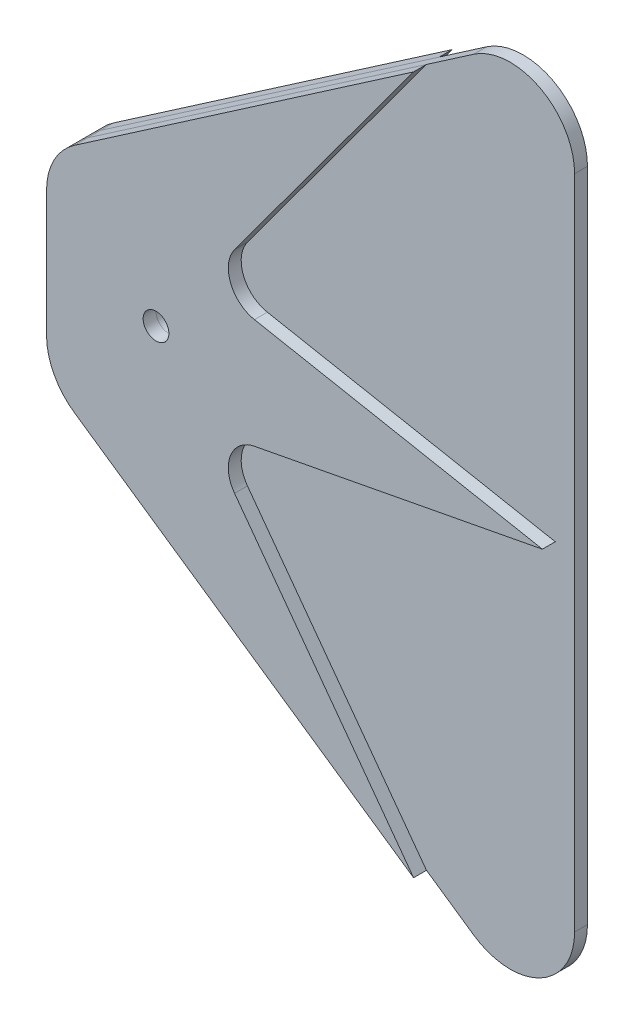
SolidWorks part; units mm, degrees
material "Silicon Rubber"
ref_plane "Front Plane" through (0, 0, 0) normal (0, 0, 1) x (1, 0, 0)
ref_plane "Top Plane" through (0, 0, 0) normal (0, 1, 0) x (1, 0, 0)
ref_plane "Right Plane" through (0, 0, 0) normal (1, 0, 0) x (0, 0, -1)
sketch "Sketch1" plane through (0, 0, 0) normal (0, 0, 1) x (1, 0, 0)
  line L0 (-17, 9.7397) -> (-17, -9.7397)
  line L1 (-12.6653, -17.9801) -> (47.3347, -59.2301)
  line L2 (63, -50.9897) -> (63, 50.9897)
  line L3 (47.3347, 59.2301) -> (-12.6653, 17.9801)
  circle A0 centre (0, 0) radius 2
  arc A1 (47.3347, -59.2301) -> (63, -50.9897) centre (53, -50.9897) ccw
  arc A2 (63, 50.9897) -> (47.3347, 59.2301) centre (53, 50.9897) ccw
  arc A3 (-17, -9.7397) -> (-12.6653, -17.9801) centre (-7, -9.7397) ccw
  arc A4 (-17, 9.7397) -> (-12.6653, 17.9801) centre (-7, 9.7397) cw
  point P7 (63, 0)
  point P9 (-17, 0)
  point P12 (63, -70)
  point P15 (63, 70)
  point P18 (-17, -15)
  point P21 (-17, 15)
  dimension "D1" = 4
  dimension "D6" = 10
  dimension "D2" = 30
  dimension "D3" = 140
  dimension "D4" = 17
  dimension "D5" = 80
extrude "Boss-Extrude1" add sketch "Sketch1" along normal mid plane 2
sketch "Sketch2" plane through (0, 0, 1) normal (0, 0, 1) x (1, 0, 0)
  line L0 (-17, 9.7397) -> (-17, -9.7397) construction
  line L1 (-17, 9.7397) -> (-17, -9.7397)
  line L2 (-12.6653, 17.9801) -> (40, 54.1875)
  line L3 (47.3347, 59.2301) -> (-12.6653, 17.9801) construction
  line L4 (12.1998, 16.39) -> (40, 54.1875)
  line L5 (15.2921, 8.5158) -> (60, 0)
  line L6 (12.1998, -16.39) -> (40, -54.1875)
  line L7 (-12.6653, -17.9801) -> (47.3347, -59.2301) construction
  line L8 (40, -54.1875) -> (-12.6653, -17.9801)
  line L9 (60, 0) -> (15.2921, -8.5158)
  arc A0 (-17, -9.7397) -> (-12.6653, -17.9801) centre (-7, -9.7397) ccw construction
  arc A1 (-12.6653, 17.9801) -> (-17, 9.7397) centre (-7, 9.7397) ccw construction
  arc A2 (-17, -9.7397) -> (-12.6653, -17.9801) centre (-7, -9.7397) ccw
  arc A3 (-12.6653, 17.9801) -> (-17, 9.7397) centre (-7, 9.7397) ccw
  arc A4 (15.2921, -8.5158) -> (12.1998, -16.39) centre (16.2277, -13.4275) ccw
  arc A5 (12.1998, 16.39) -> (15.2921, 8.5158) centre (16.2277, 13.4275) ccw
  circle A6 centre (0, 0) radius 2 construction
  circle A7 centre (0, 0) radius 2
  point P22 (7.5, -10)
  point P25 (7.5, 10)
  dimension "D1" = 40
  dimension "D5" = 5
  dimension "D2" = 20
  dimension "D3" = 7.5
  dimension "D4" = 60
extrude "Boss-Extrude2" add sketch "Sketch2" along normal blind 2 separate body
mirror "Mirror1" about plane through (0, 0, 0) normal (0, 0, 1) of bodies 102
